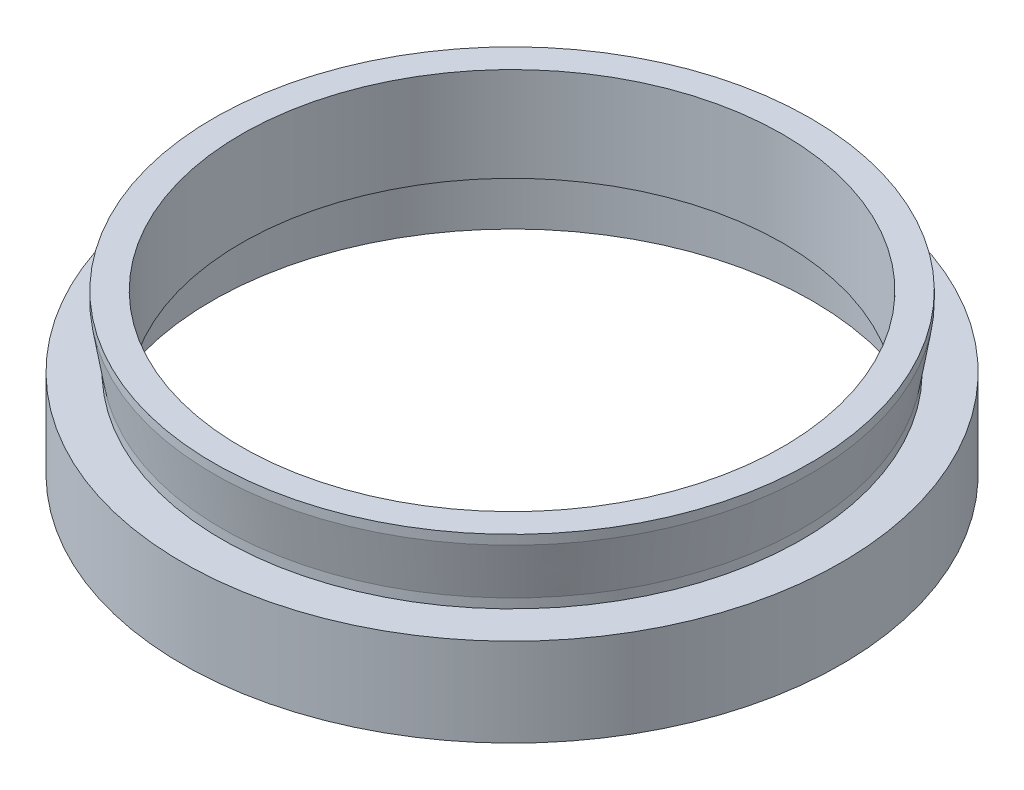
SolidWorks part; units mm, degrees
ref_plane "前视基准面" through (0, 0, 0) normal (0, 0, 1) x (1, 0, 0)
ref_plane "上视基准面" through (0, 0, 0) normal (0, 1, 0) x (1, 0, 0)
ref_plane "右视基准面" through (0, 0, 0) normal (1, 0, 0) x (0, 0, -1)
sketch "草图1" plane through (0, 0, 0) normal (0, 0, 1) x (1, 0, 0)
  line L0 (0, 0) -> (0, 73.2965) construction
  line L1 (-23, 5) -> (-23, 13)
  line L2 (-23, 13) -> (-25.365, 13)
  line L3 (-25.365, 13) -> (-25.365, 12.2)
  line L4 (-25.365, 12.2) -> (-24.635, 7.8)
  line L5 (-24.635, 7.8) -> (-24.635, 7)
  line L6 (-24.635, 7) -> (-28, 7)
  line L7 (-28, 7) -> (-28, -0.5)
  line L12 (-28, -0.5) -> (-25.5, -0.5)
  line L13 (-23, 5) -> (-26.5, 5)
  line L14 (-26.5, 5) -> (-26.5, 4)
  line L15 (-26.5, 4) -> (-25.5, 4)
  line L16 (-25.5, 4) -> (-25.5, -0.5)
  dimension "D1" = 23
  dimension "D2" = 25.365
  dimension "D3" = 24.635
  dimension "D4" = 28
  dimension "D6" = 13.5
  dimension "D7" = 6
  dimension "D9" = 25.5
  dimension "D10" = 0.8
  dimension "D11" = 0.8
  dimension "D14" = 1
  dimension "D15" = 26.5
revolve "旋转1" add sketch "草图1" angle 360 about L0
cosmetic thread "装饰螺纹线1" parameters "D1"=9, "D2"=47
cosmetic thread "装饰螺纹线2" parameters "D2"=52
